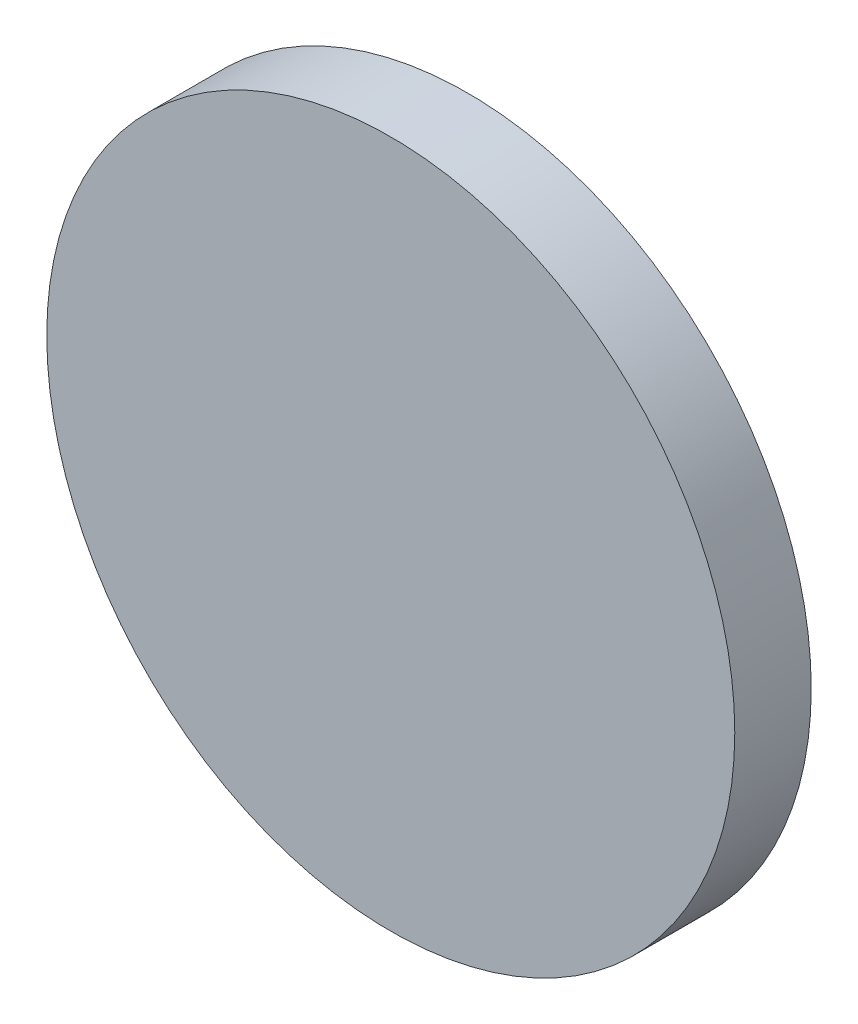
SolidWorks part; units mm, degrees
ref_plane "Front Plane" through (0, 0, 0) normal (0, 0, 1) x (1, 0, 0)
ref_plane "Top Plane" through (0, 0, 0) normal (0, 1, 0) x (1, 0, 0)
ref_plane "Right Plane" through (0, 0, 0) normal (1, 0, 0) x (0, 0, -1)
sketch "Sketch1" plane through (0, 0, 0) normal (0, 0, 1) x (1, 0, 0)
  circle A0 centre (0, 0) radius 9
  dimension "D1" = 18
extrude "Boss-Extrude1" add sketch "Sketch1" along normal blind 2
